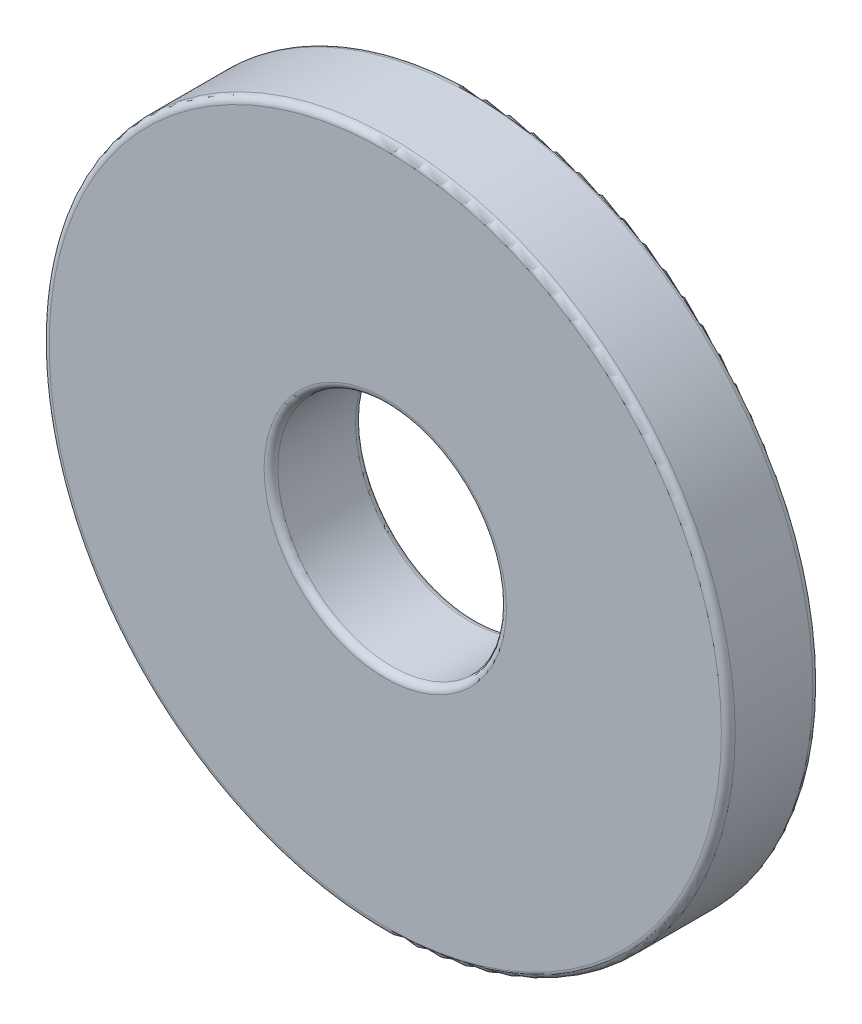
SolidWorks part; units mm, degrees
material "Chrome Stainless Steel"
ref_plane "Front Plane" through (0, 0, 0) normal (0, 0, 1) x (1, 0, 0)
ref_plane "Top Plane" through (0, 0, 0) normal (0, 1, 0) x (1, 0, 0)
ref_plane "Right Plane" through (0, 0, 0) normal (1, 0, 0) x (0, 0, -1)
sketch "Sketch1" plane through (0, 0, 0) normal (0, 0, 1) x (1, 0, 0)
  circle A0 centre (0, 0) radius 2.5
  circle A1 centre (0, 0) radius 7.5
  dimension "D1" = 5
  dimension "D2" = 15
extrude "Boss-Extrude1" add sketch "Sketch1" along normal blind 2
fillet "Fillet1" radius 0.15 4 edges at (2.5, 0, 0) (7.5, 0, 0) (2.5, 0, 2) (7.5, 0, 2)
